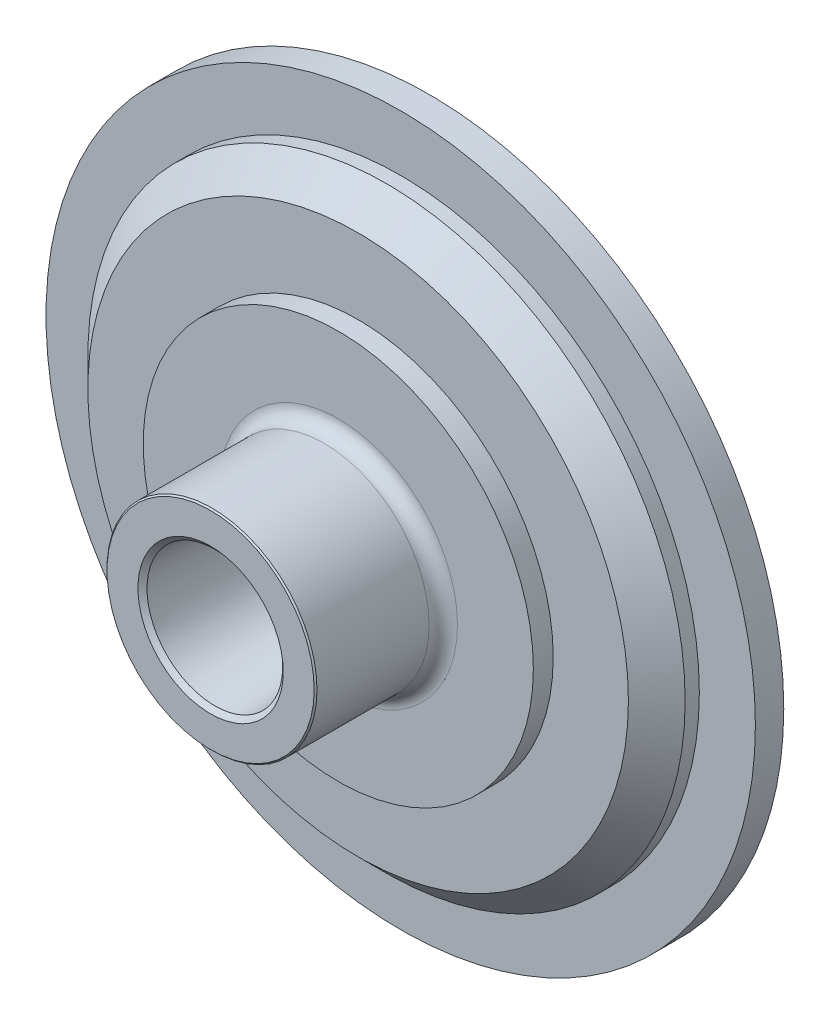
SolidWorks part; units mm, degrees
ref_plane "Спереди" through (0, 0, 0) normal (0, 0, 1) x (1, 0, 0)
ref_plane "Сверху" through (0, 0, 0) normal (0, 1, 0) x (1, 0, 0)
ref_plane "Справа" through (0, 0, 0) normal (1, 0, 0) x (0, 0, -1)
sketch "Эскиз1" plane through (0, 0, 0) normal (1, 0, 0) x (0, 0, -1)
  line L0 (5.2816, 0) -> (57.6059, 0) construction
  line L43 (65.4819, 20.76) -> (15.9788, 23.9049)
  line L44 (14.4819, 25.605) -> (14.4819, 36.5)
  line L45 (14.9819, 37) -> (54.4819, 37)
  line L46 (59.4819, 42) -> (59.4819, 68.75)
  line L47 (59.4819, 68.75) -> (66.4819, 68.75)
  line L48 (66.4819, 68.75) -> (66.4819, 95.25)
  line L49 (66.4819, 95.25) -> (76.4819, 105.25)
  line L50 (76.4819, 105.25) -> (81.4819, 105.25)
  line L51 (81.4819, 105.25) -> (81.4819, 125)
  line L52 (81.4819, 125) -> (91.4819, 125)
  line L53 (91.4819, 125) -> (91.4819, 95)
  line L54 (91.4819, 95) -> (94.4819, 95)
  line L55 (94.4819, 95) -> (94.4819, 90)
  line L56 (94.4819, 90) -> (79.4819, 90)
  line L57 (79.4819, 90) -> (79.4819, 66.15)
  line L58 (79.4819, 66.15) -> (75.9819, 66.15)
  line L59 (75.9819, 66.15) -> (75.9819, 53.1865)
  line L60 (75.9819, 53.1865) -> (65.4819, 35)
  line L61 (65.4819, 35) -> (65.4819, 20.76)
  line L63 (14.4819, 36.5) -> (14.9819, 37)
  line L64 (15.9788, 23.9049) -> (14.4819, 25.605)
  arc A0 (59.4819, 42) -> (54.4819, 37) centre (54.4819, 42) cw
  point P4 (14.4819, 24)
  point P5 (14.4819, 37)
  point P13 (48.557, -11.5592)
  point P24 (94.4819, 92.5)
  point P25 (67.7161, 12.8519)
  point P27 (-49.0461, 115.2857)
  point P28 (-45.8949, 85.8751)
  point P29 (94.836, 53.1865)
  point P35 (14.4819, 24)
  point P36 (15.1625, 20.1684)
  dimension "D12" = 95
  dimension "D9" = 5
  dimension "D1" = 125
  dimension "D2" = 105.25
  dimension "D3" = 95.25
  dimension "D4" = 45
  dimension "D5" = 68.75
  dimension "D6" = 37
  dimension "D7" = 24
  dimension "D8" = 45
  dimension "D10" = 7
  dimension "D11" = 5
  dimension "D13" = 3
  dimension "D14" = 26
  dimension "D15" = 30
  dimension "D16" = 66.15
  dimension "D17" = 90
  dimension "D18" = 3.5
  dimension "D19" = 0.5
  dimension "D20" = 35
  dimension "D21" = 20.76
  dimension "D22" = 10
  dimension "D23" = 15
  dimension "D25" = 1.5
  dimension "D26" = 45
  dimension "D24" = 45
revolve "Повернуть2" add sketch "Эскиз1" angle 360 about L0
